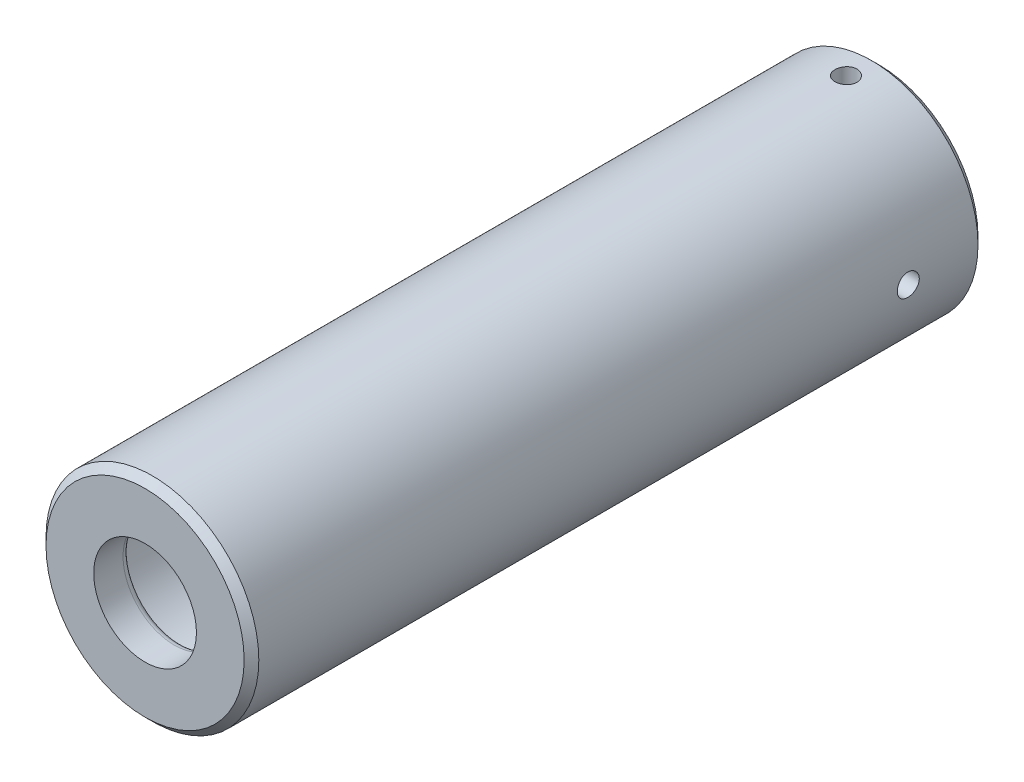
SolidWorks part; units mm, degrees
ref_plane "Plan de face" through (0, 0, 0) normal (0, 0, 1) x (1, 0, 0)
ref_plane "Plan de dessus" through (0, 0, 0) normal (0, 1, 0) x (1, 0, 0)
ref_plane "Plan de droite" through (0, 0, 0) normal (1, 0, 0) x (0, 0, -1)
sketch "Esquisse1" plane through (0, 0, 0) normal (1, 0, 0) x (0, 0, -1)
  line L0 (-50, 0) -> (50, 0) construction
  line L1 (-45, 11) -> (-45, 7)
  line L2 (-50, 14.5) -> (50, 14.5)
  line L3 (-50, 14.5) -> (-50, 7)
  line L4 (-45, 11) -> (50, 11)
  line L5 (50, 14.5) -> (50, 11)
  line L6 (-50, 0) -> (-50, 1.75) construction
  line L7 (-50, 1.75) -> (-30, 1.75) construction
  line L8 (-30, 1.75) -> (-30, 0) construction
  line L9 (-50, 7) -> (-45, 7)
  dimension "D1" = 11
  dimension "D2" = 14.5
  dimension "D3" = 100
  dimension "D4" = 5
  dimension "D5" = 1.75
  dimension "D6" = 20
  dimension "D7" = 4
revolve "Révolution1" add sketch "Esquisse1" angle 360 about L0
sketch "Esquisse2" plane through (0, 0, 0) normal (1, 0, 0) x (0, 0, -1)
  line L0 (50, -14.5) -> (50, 14.5) construction
  circle A0 centre (39.5, 0) radius 1.5
  point P2 (0, 0)
  dimension "D1" = 3
  dimension "D2" = 10.5
extrude "Enlèv. mat.-Extru.1" cut sketch "Esquisse2" against normal through all both and the other way through all
sketch "Esquisse3" plane through (0, 0, 0) normal (0, 1, 0) x (1, 0, 0)
  line L0 (11, 50) -> (-11, 50) construction
  circle A0 centre (0, 45.5) radius 1.5
  dimension "D1" = 3
  dimension "D2" = 4.5
extrude "Enlèv. mat.-Extru.2" cut sketch "Esquisse3" against normal through all both and the other way through all
fillet "Congé1" radius 2 1 edges at (11, 0, 45)
fillet "Congé2" radius 1 1 edges at (7, 0, 45)
chamfer "Chanfrein1" distance 1 angle 45 2 edges at (14.5, 0, -50) (14.5, 0, 50)
